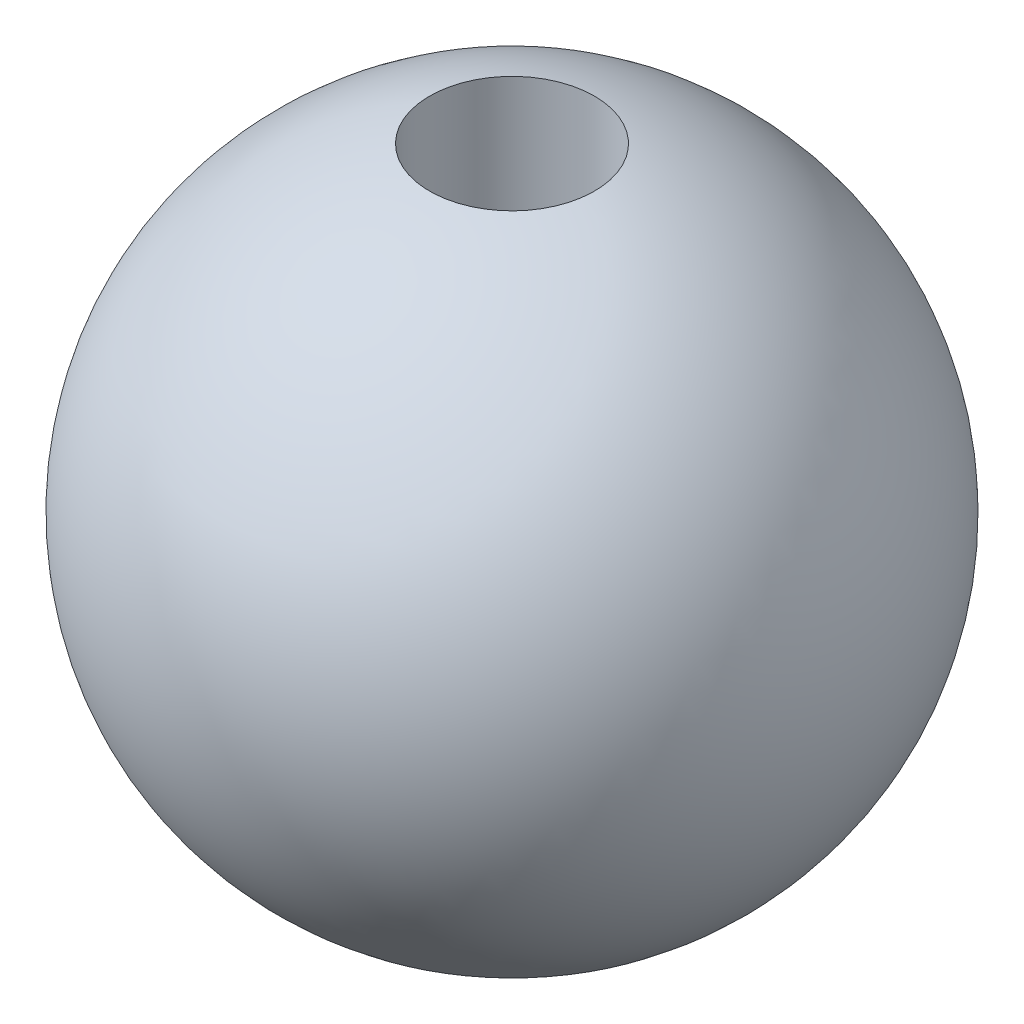
SolidWorks part; units mm, degrees
ref_plane "Front" through (0, 0, 0) normal (0, 0, 1) x (1, 0, 0)
ref_plane "Top" through (0, 0, 0) normal (0, 1, 0) x (1, 0, 0)
ref_plane "Right" through (0, 0, 0) normal (1, 0, 0) x (0, 0, -1)
sketch "Sketch1" plane through (0, 0, 0) normal (0, 1, 0) x (1, 0, 0)
  line L0 (0, 11.5949) -> (0, -9.4083) construction
  circle A0 centre (0, 0) radius 6
  dimension "D1" = 12
revolve "Revolve3" add sketch "Sketch1" angle 360 about L0
sketch "Sketch2" plane through (0, 0, 0) normal (0, 1, 0) x (1, 0, 0)
  circle A0 centre (0, 0) radius 1.5
  dimension "D1" = 3
extrude "Cut-Extrude1" cut sketch "Sketch2" along normal through all
